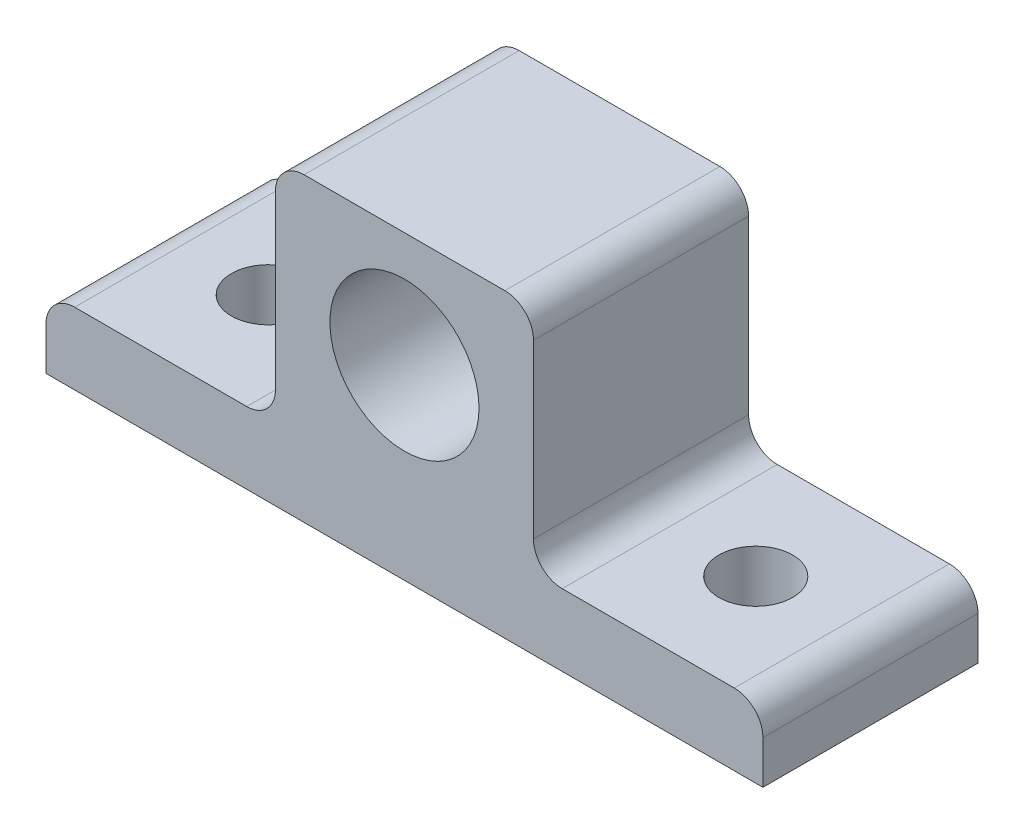
SolidWorks part; units mm, degrees
ref_plane "Front Plane" through (0, 0, 0) normal (0, 0, 1) x (1, 0, 0)
ref_plane "Top Plane" through (0, 0, 0) normal (0, 1, 0) x (1, 0, 0)
ref_plane "Right Plane" through (0, 0, 0) normal (1, 0, 0) x (0, 0, -1)
sketch "Sketch1" plane through (0, 0, 0) normal (0, 1, 0) x (1, 0, 0)
  line L1 (-35.381, 3.1139) -> (28.119, 3.1139)
  line L2 (-35.381, 3.1139) -> (-35.381, -15.9361)
  line L3 (-35.381, -15.9361) -> (28.119, -15.9361)
  line L4 (28.119, 3.1139) -> (28.119, -15.9361)
  line L5 (-17.601, 3.1139) -> (10.339, 3.1139)
  line L6 (-17.601, 3.1139) -> (-17.601, -15.9361)
  line L7 (-17.601, -15.9361) -> (10.339, -15.9361)
  line L8 (10.339, 3.1139) -> (10.339, -15.9361)
  circle A0 centre (-25.221, -6.4111) radius 3.2639
  circle A1 centre (17.959, -6.4111) radius 3.2639
  dimension "D7" = 6.5278
  dimension "D8" = 6.5278
  dimension "D1" = 19.05
  dimension "D2" = 63.5
  dimension "D3" = 10.16
  dimension "D4" = 10.16
  dimension "D5" = 9.525
  dimension "D6" = 9.525
  dimension "D9" = 7.62
  dimension "D10" = 7.62
extrude "Boss-Extrude3" add sketch "Sketch1" along normal blind 6.35 contours L6 L1 L2 L3 A0 | L8 L1 L6 L3 | L1 L8 L3 L4 A1
sketch "Sketch3" plane through (0, 6.35, 0) normal (0, 1, 0) x (1, 0, 0)
  line L0 (-35.381, -15.9361) -> (28.119, -15.9361) construction
  line L1 (-15.061, -15.9361) -> (7.799, -15.9361)
  line L2 (-15.061, -15.9361) -> (-15.061, 3.1139)
  line L3 (-15.061, 3.1139) -> (7.799, 3.1139)
  line L4 (7.799, -15.9361) -> (7.799, 3.1139)
  line L5 (-35.381, 3.1139) -> (28.119, 3.1139) construction
  circle A0 centre (-25.221, -6.4111) radius 3.2639 construction
  circle A1 centre (17.959, -6.4111) radius 3.2639 construction
  dimension "D1" = 10.16
  dimension "D2" = 10.16
extrude "Boss-Extrude4" add sketch "Sketch3" along normal blind 20.32
sketch "Sketch6" plane through (0, 0, 15.9361) normal (0, 0, 1) x (1, 0, 0)
  line L0 (7.799, 26.67) -> (7.799, 6.35) construction
  line L2 (-15.061, 26.67) -> (7.799, 26.67) construction
  circle A0 centre (-3.631, 16.51) radius 6.604
  dimension "D3" = 13.208
  dimension "D1" = 11.43
  dimension "D2" = 10.16
extrude "Cut-Extrude1" cut sketch "Sketch6" against normal blind 20.32
fillet "Fillet5" radius 2.54 6 edges at (-35.381, 6.35, 6.4111) (28.119, 6.35, 6.4111) (7.799, 26.67, 6.4111) (-15.061, 26.67, 6.4111)
